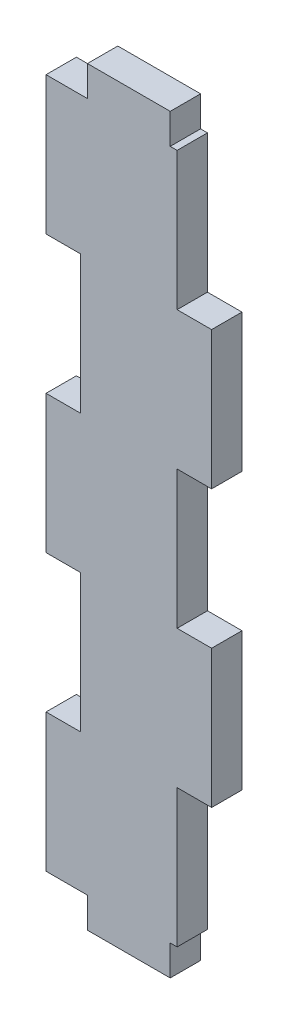
SolidWorks part; units mm, degrees
ref_plane "前视基准面" through (0, 0, 0) normal (0, 0, 1) x (1, 0, 0)
ref_plane "上视基准面" through (0, 0, 0) normal (0, 1, 0) x (1, 0, 0)
ref_plane "右视基准面" through (0, 0, 0) normal (1, 0, 0) x (0, 0, -1)
sketch "草图1" plane through (0, 0, 0) normal (0, 0, 1) x (1, 0, 0)
  line L0 (6, 50) -> (6, 54.4)
  line L1 (-7, -50) -> (-6, -50)
  line L2 (-7, -50) -> (-7, 50) construction
  line L3 (-7, 50) -> (-6, 50)
  line L4 (7, -50) -> (7, 50) construction
  line L5 (0, 50) -> (0, -50) construction
  line L6 (-7, 0) -> (7, 0) construction
  line L7 (6, 54.4) -> (-6, 54.4)
  line L8 (-6, 50) -> (-6, 54.4)
  line L9 (6, -50) -> (6, -54.4)
  line L10 (-6, -50) -> (-6, -54.4)
  line L11 (6, -54.4) -> (-6, -54.4)
  line L12 (6, 50) -> (7, 50)
  line L13 (6, -50) -> (7, -50)
  line L14 (7, 30) -> (12, 30)
  line L15 (12, 30) -> (12, 10)
  line L16 (12, 10) -> (7, 10)
  line L17 (12, -30) -> (7, -30)
  line L18 (12, -10) -> (12, -30)
  line L19 (7, -10) -> (12, -10)
  line L20 (-7, 50) -> (-12, 50)
  line L21 (-12, 50) -> (-12, 30)
  line L22 (-12, 30) -> (-7, 30)
  line L23 (-7, 10) -> (-12, 10)
  line L24 (-12, 10) -> (-12, -10)
  line L25 (-12, -10) -> (-7, -10)
  line L26 (-7, -30) -> (-12, -30)
  line L27 (-12, -30) -> (-12, -50)
  line L28 (-12, -50) -> (-7, -50)
  line L29 (-7, -30) -> (-7, -10)
  line L30 (7, -10) -> (7, 10)
  line L31 (7, -30) -> (7, -50)
  line L32 (-7, 30) -> (-7, 10)
  line L33 (7, 50) -> (7, 30)
  point P0 (0, 0)
  point P11 (0, 54.4)
  point P15 (0, -54.4)
  dimension "D1" = 100
  dimension "D2" = 12
  dimension "D3" = 4.4
  dimension "D4" = 14
  dimension "D5" = 7
  dimension "D6" = 20
  dimension "D7" = 5
  dimension "D8" = 20
  dimension "D10" = 5
  dimension "D11" = 20
  dimension "D9" = 2
  dimension "D12" = 3
extrude "凸台-拉伸1" add sketch "草图1" along normal blind 4.4
